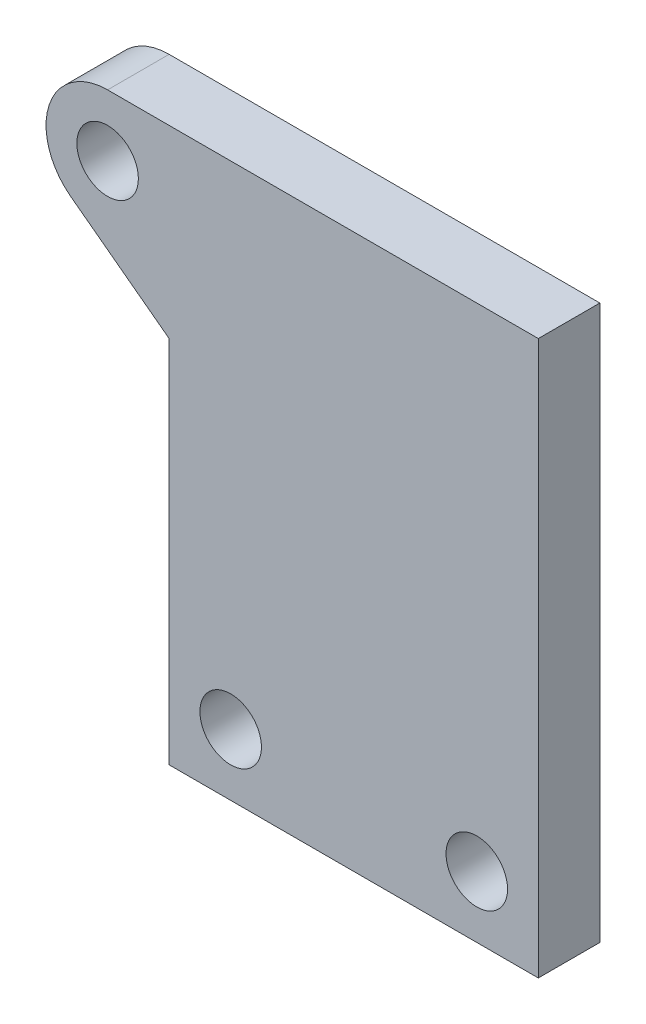
SolidWorks part; units mm, degrees
material "Plain Carbon Steel"
ref_plane "Front Plane" through (0, 0, 0) normal (0, 0, 1) x (1, 0, 0)
ref_plane "Top Plane" through (0, 0, 0) normal (0, 1, 0) x (1, 0, 0)
ref_plane "Right Plane" through (0, 0, 0) normal (1, 0, 0) x (0, 0, -1)
sketch "Sketch1" plane through (0, 0, 0) normal (0, 0, 1) x (1, 0, 0)
  line L0 (-10, 0) -> (10, 0) construction
  line L1 (-15, -5) -> (15, -5)
  line L2 (-15, -5) -> (-15, 25)
  line L4 (15, -5) -> (15, 40)
  line L5 (-15, 25) -> (-25, 25) construction
  line L10 (-25, 25) -> (-25, 35) construction
  line L11 (-20, 40) -> (15, 40)
  line L14 (-15, 25) -> (-23, 31)
  circle A0 centre (-10, 0) radius 2.5
  circle A1 centre (10, 0) radius 2.5
  circle A2 centre (-20, 35) radius 2.5
  arc A3 (-25, 35) -> (-20, 40) centre (-20, 35) cw
  arc A4 (-25, 35) -> (-23, 31) centre (-20, 35) ccw
  point P9 (0, -5)
  point P18 (-25, 40)
  dimension "D2" = 5
  dimension "D8" = 5
  dimension "D11" = 5
  dimension "D1" = 20
  dimension "D3" = 5
  dimension "D4" = 30
  dimension "D5" = 30
  dimension "D6" = 15
  dimension "D7" = 10
  dimension "D9" = 5
  dimension "D10" = 5
extrude "Boss-Extrude1" add sketch "Sketch1" along normal blind 5
